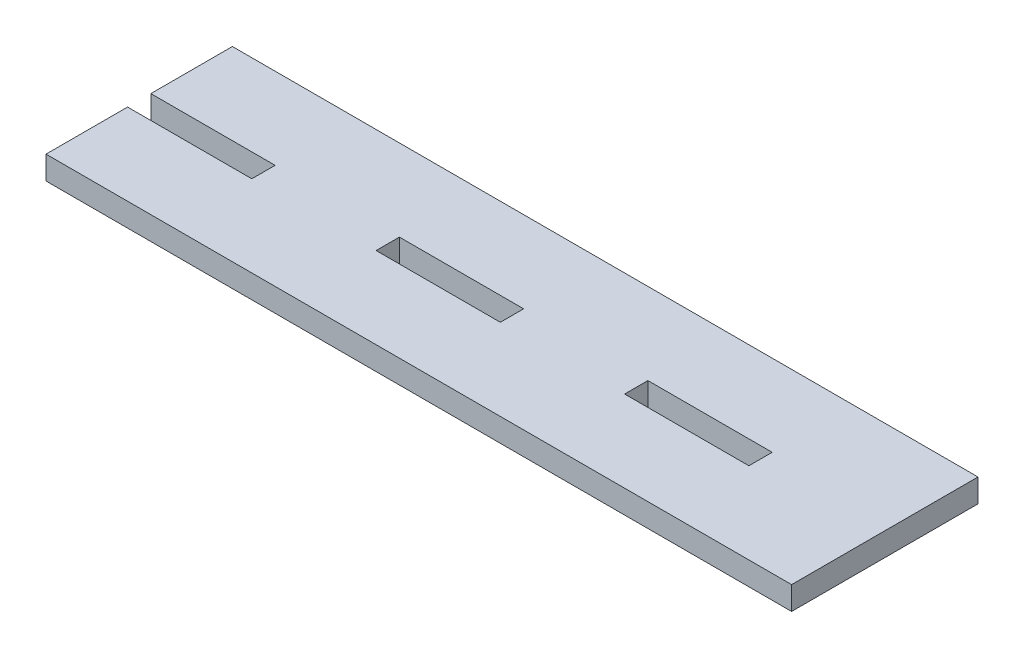
SolidWorks part; units mm, degrees
material "Foam#1"
ref_plane "Front Plane" through (0, 0, 0) normal (0, 0, 1) x (1, 0, 0)
ref_plane "Top Plane" through (0, 0, 0) normal (0, 1, 0) x (1, 0, 0)
ref_plane "Right Plane" through (0, 0, 0) normal (1, 0, 0) x (0, 0, -1)
sketch "Sketch1" plane through (0, 0, 0) normal (0, 1, 0) x (1, 0, 0)
  line L0 (-76.2, 2.3813) -> (-76.2, -2.3813)
  line L1 (-76.2, -19.05) -> (76.2, -19.05)
  line L2 (-76.2, -19.05) -> (-76.2, 19.05)
  line L3 (-76.2, 19.05) -> (76.2, 19.05)
  line L4 (76.2, -19.05) -> (76.2, 19.05)
  line L5 (-76.2, -19.05) -> (76.2, 19.05) construction
  line L6 (-76.2, 19.05) -> (76.2, -19.05) construction
  line L7 (-25.4, -2.3813) -> (-25.4, 2.3813)
  line L8 (-76.2, -2.3813) -> (-50.8, -2.3813)
  line L9 (-76.2, -2.3813) -> (-76.2, 2.3813)
  line L10 (-76.2, 2.3813) -> (-50.8, 2.3813)
  line L11 (-50.8, -2.3813) -> (-50.8, 2.3813)
  line L12 (-25.4, -2.3813) -> (0, -2.3813)
  line L13 (0, -2.3813) -> (0, 2.3813)
  line L14 (-25.4, 2.3813) -> (0, 2.3813)
  line L15 (25.4, -2.3813) -> (25.4, 2.3813)
  line L16 (25.4, -2.3813) -> (50.8, -2.3813)
  line L17 (50.8, -2.3813) -> (50.8, 2.3813)
  line L18 (25.4, 2.3813) -> (50.8, 2.3813)
  point P0 (0, 0)
  point P9 (-76.2, 0)
  dimension "D1" = 152.4
  dimension "D2" = 38.1
  dimension "D3" = 4.7625
  dimension "D4" = 25.4
  dimension "D5" = 3
extrude "Boss-Extrude1" add sketch "Sketch1" along normal blind 4.7625
